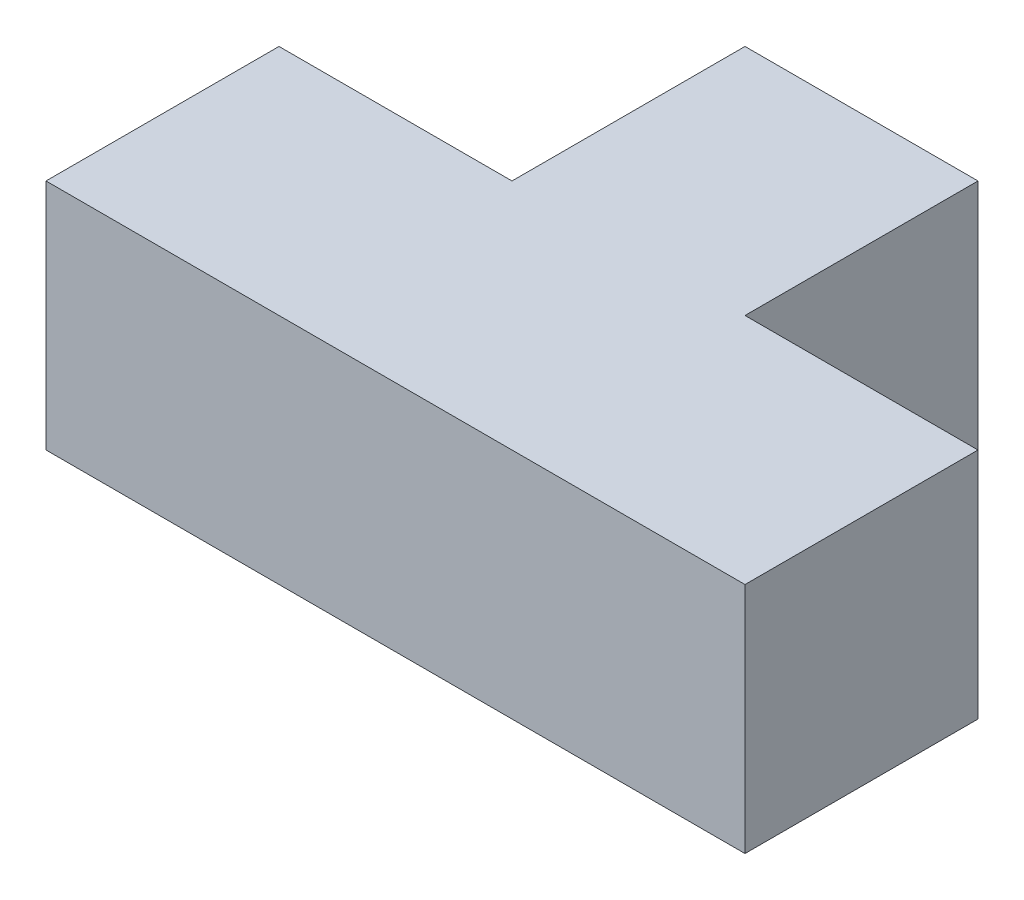
SolidWorks part; units mm, degrees
ref_plane "Alzado" through (0, 0, 0) normal (0, 0, 1) x (1, 0, 0)
ref_plane "Planta" through (0, 0, 0) normal (0, 1, 0) x (1, 0, 0)
ref_plane "Vista lateral" through (0, 0, 0) normal (1, 0, 0) x (0, 0, -1)
sketch "Croquis1" plane through (0, 0, 0) normal (0, 1, 0) x (1, 0, 0)
  line L0 (400, 200) -> (600, 200)
  line L1 (0, 0) -> (600, 0)
  line L2 (0, 0) -> (0, 200)
  line L3 (0, 200) -> (200, 200)
  line L4 (600, 0) -> (600, 200)
  line L6 (200, 200) -> (200, 400)
  line L7 (200, 400) -> (400, 400)
  line L8 (400, 200) -> (400, 400)
  dimension "D1" = 200
  dimension "D2" = 200
  dimension "D3" = 200
  dimension "D4" = 200
  dimension "D5" = 200
extrude "Saliente-Extruir1" add sketch "Croquis1" along normal blind 200
